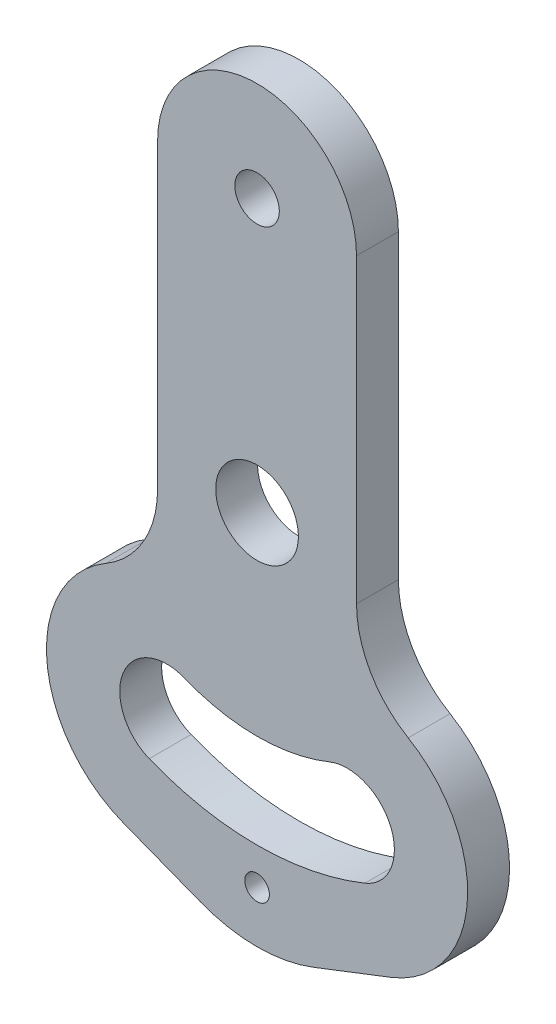
SolidWorks part; units mm, degrees
ref_plane "Спереди" through (0, 0, 0) normal (0, 0, 1) x (1, 0, 0)
ref_plane "Сверху" through (0, 0, 0) normal (0, 1, 0) x (1, 0, 0)
ref_plane "Справа" through (0, 0, 0) normal (1, 0, 0) x (0, 0, -1)
sketch "Эскиз1" plane through (0, 0, 0) normal (0, 0, 1) x (1, 0, 0)
  line L0 (0, 125.6261) -> (0, -12) construction
  line L3 (-17.2319, 19.3495) -> (0, 62) construction
  line L4 (0, 62) -> (17.2319, 19.3495) construction
  line L5 (17.2319, 19.3495) -> (0, 62) construction
  line L8 (-19, 114) -> (-19, 56.4326)
  line L9 (-25.5465, -2.095) -> (0, -12)
  line L10 (25.5465, -2.095) -> (0, -12)
  line L11 (19, 114) -> (19, 56.4326)
  circle A2 centre (0, 62) radius 7.9
  circle A3 centre (0, 114) radius 4.25
  circle A4 centre (0, 0) radius 2.35
  arc A5 (-17.2319, 19.3495) -> (17.2319, 19.3495) centre (0, 62) ccw construction
  arc A6 (-20.6034, 11.0049) -> (20.6034, 11.0049) centre (0, 62) ccw
  arc A7 (-13.8604, 27.6942) -> (13.8604, 27.6942) centre (0, 62) ccw
  arc A8 (-13.8604, 27.6942) -> (-20.6034, 11.0049) centre (-17.2319, 19.3495) ccw
  arc A9 (20.6034, 11.0049) -> (13.8604, 27.6942) centre (17.2319, 19.3495) ccw
  arc A12 (-28.8753, 39.1846) -> (-25.5465, -2.095) centre (-17.2319, 19.3495) ccw
  arc A13 (-19, 114) -> (19, 114) centre (0, 114) cw
  arc A14 (28.8753, 39.1846) -> (25.5465, -2.095) centre (17.2319, 19.3495) cw
  arc A15 (28.8753, 39.1846) -> (19, 56.4326) centre (39, 56.4326) cw
  arc A16 (-19, 56.4326) -> (-28.8753, 39.1846) centre (-39, 56.4326) cw
  point P17 (0, 16)
  point P30 (19, 42.2815)
  point P34 (-19, 42.2815)
  dimension "D1" = 8.5
  dimension "D2" = 15.8
  dimension "D3" = 4.7
  dimension "D7" = 9
  dimension "D6" = 38
  dimension "D10" = 23
  dimension "D12" = 20
  dimension "D4" = 52
  dimension "D5" = 62
  dimension "D8" = 46
  dimension "D9" = 44
  dimension "D11" = 12
extrude "Бобышка-Вытянуть1" add sketch "Эскиз1" along normal blind 8
fillet "Скругление1" radius 30 1 edges at (0, -12, 4)
